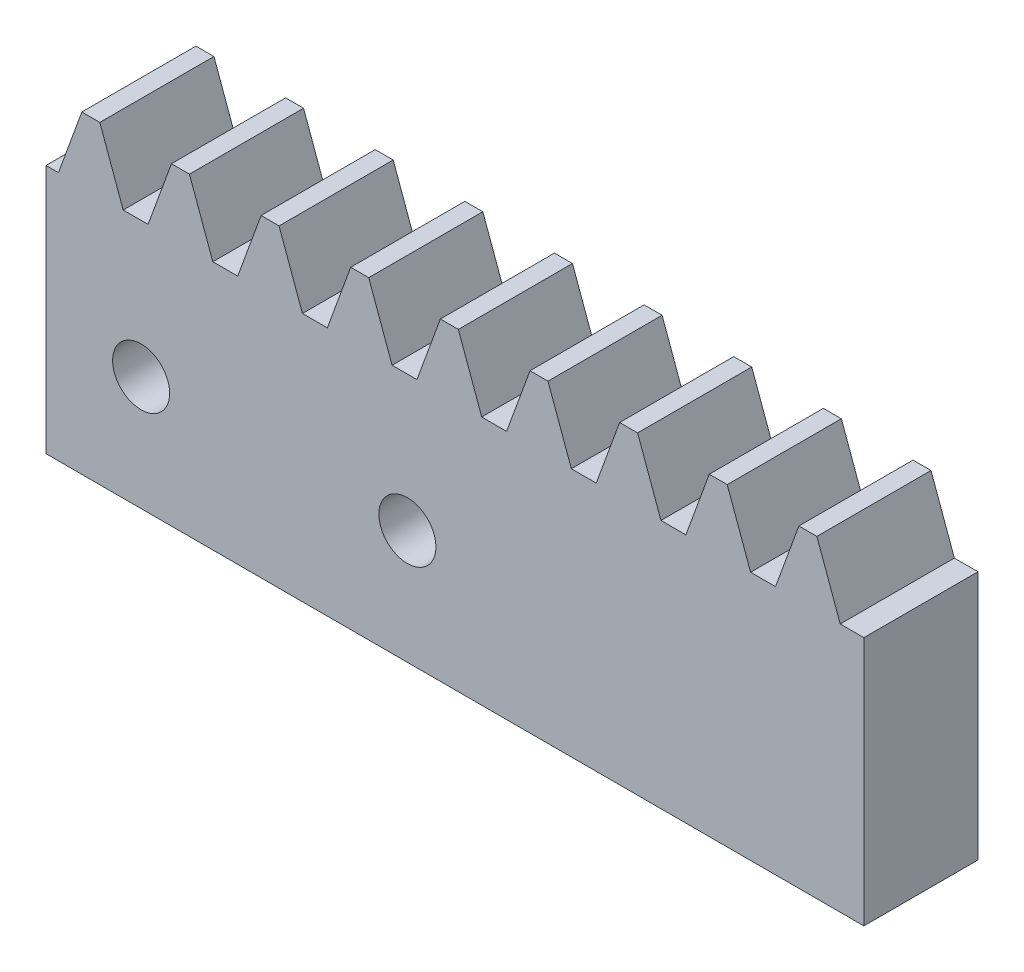
SolidWorks part; units mm, degrees
extrude "Blank" add sketch "BlankSke" against normal blind 6
sketch "BlankSke" plane through (0, 0, 0) normal (0, 0, 1) x (1, 0, 0)
  line L1 (0, 0) -> (43, 0)
  line L2 (0, 0) -> (0, 16.5)
  line L3 (0, 16.5) -> (43, 16.5)
  line L4 (43, 0) -> (43, 16.5)
  dimension "Length" = 43
  dimension "Blank_height" = 16.5
ref_plane "Plane1" through (0, 0, 0) normal (0, 0, 1) x (1, 0, 0)
ref_plane "Plane2" through (0, 0, 0) normal (0, 1, 0) x (1, 0, 0)
ref_plane "Plane3" through (0, 0, 0) normal (1, 0, 0) x (0, 0, -1)
sketch "HoldingSke" plane through (0, 0, 0) normal (0, 1, 0) x (1, 0, 0)
  line L0 (0, 0) -> (0.0928, 0.6602)
  line L1 (-15, 0) -> (100, 0) construction
  line L2 (0, 0) -> (-2.1039, 2.3779)
  line L3 (0, 0) -> (-11.863, 4.5341)
  line L4 (0, 0) -> (8.4773, 1.6478)
  line L5 (0, 0) -> (-23.7986, -8.8762)
  line L6 (0, 0) -> (-10.5278, -7.1032)
  line L9 (-71.009, 38.7566) -> (-30.6022, 53.4635)
  line L10 (-76.2, 3.8779) -> (-61.2, 3.8779)
  line L11 (0, 0) -> (-6, 0)
  line L12 (-76.2, 101.6) -> (-76.147, 101.6)
  line L13 (24.9733, 27.94) -> (52.9518, 28.4284)
  line L14 (24.9733, 27.94) -> (24.9743, 27.94)
  line L15 (24.9733, 27.94) -> (100.4006, 29.5858)
  circle A0 centre (0, 0) radius 19.05
  circle A1 centre (0, 0) radius 7.5
  circle A2 centre (0, 0) radius 12.7
  dimension "MPH" = 15
  dimension "Diameter" = 38.1
  dimension "Num_teeth" = 11
  dimension "Pitch" = 0.6667
  dimension "Show_teeth" = 998
  dimension "Thickness" = 12.7
  dimension "Ap" = 20
  dimension "Pitch_height" = 15
  dimension "Width" = 6
  dimension "Backlash" = 0.053
  dimension "Addendum_fac" = 1
  dimension "Dedendum_fac" = 1.25
  dimension "Clearance_fac" = 0.25
  dimension "Dedendum_add" = 0.001
  dimension "Length" = 43
  dimension "Module" = 1.5
sketch "TooCutSkeIll" plane through (0, 0, 0) normal (0, 0, 1) x (1, 0, 0)
  line L0 (-1.8687, 16.4605) -> (-0.7447, 13.3724)
  line L1 (-0.3914, 13.125) -> (0.3914, 13.125)
  line L2 (0.7447, 13.3724) -> (1.8687, 16.4605)
  line L3 (43, 16.5) -> (0, 16.5) construction
  line L4 (0, 0) -> (0, 64.897) construction
  line L5 (-13.208, 15) -> (12.954, 15) construction
  line L6 (0, 0) -> (43, 0) construction
  line L7 (1.3371, 15) -> (1.3371, 48.7463) construction
  line L8 (-1.3371, 15) -> (-1.3371, 48.7463) construction
  line L9 (1.9251, 16.5) -> (1.9251, 16.5254)
  line L10 (-1.9251, 16.5) -> (-1.9251, 16.5254)
  line L11 (-1.9251, 16.5254) -> (1.9251, 16.5254)
  arc A0 (0.3914, 13.125) -> (0.7447, 13.3724) centre (0.3914, 13.501) ccw
  arc A1 (-0.7447, 13.3724) -> (-0.3914, 13.125) centre (-0.3914, 13.501) ccw
  arc A2 (1.9251, 16.5) -> (1.8687, 16.4605) centre (1.9251, 16.44) ccw
  arc A3 (-1.8687, 16.4605) -> (-1.9251, 16.5) centre (-1.9251, 16.44) ccw
  dimension "Pitch_height" = 15
  dimension "Addendum_plus" = 1.5254
  dimension "Pressure_angle" = 20
  dimension "Gap_width" = 2.6742
  dimension "Dedendum" = 1.875
extrude "ToothCutIll" [suppressed] cut sketch "TooCutSkeIll" against normal through all
sketch "TooCutSkeSim" plane through (0, 0, 0) normal (0, 0, 1) x (1, 0, 0)
  line L0 (0.6547, 13.125) -> (-0.6547, 13.125)
  line L1 (1.8923, 16.5254) -> (0.6547, 13.125)
  line L2 (0, 17.4625) -> (0, 53.467) construction
  line L3 (1.8923, 16.5254) -> (-1.8923, 16.5254)
  line L6 (-1.8923, 16.5254) -> (-0.6547, 13.125)
  line L9 (-1.3371, 15) -> (1.3371, 15) construction
  line L10 (0, 0) -> (43, 0) construction
  line L11 (1.3371, 15) -> (1.3371, 53.467) construction
  line L12 (-1.3371, 15) -> (-1.3371, 53.467) construction
  dimension "Pitch_height" = 15
  dimension "Addendum_plus" = 1.5254
  dimension "Pressure_angle" = 20
  dimension "Gap_width" = 2.6742
  dimension "Dedendum" = 1.875
extrude "ToothCutSim" cut sketch "TooCutSkeSim" against normal through all
pattern_linear "TeethCuts" count 10 spacing 4.7124 along (1, 0, 0) of "ToothCutIll", "ToothCutSim"
sketch "Esquisse1" plane through (0, 0, 0) normal (0, 0, 1) x (1, 0, 0)
  line L0 (0, 13.125) -> (0, 0) construction
  line L1 (0, 0) -> (43, 0) construction
  circle A0 centre (5, 6) radius 1.5
  circle A1 centre (19, 6) radius 1.5
  dimension "D1" = 14
  dimension "D4" = 3
  dimension "D5" = 3
  dimension "D2" = 5
  dimension "D3" = 6
extrude "Enlèv. mat.-Extru.1" cut sketch "Esquisse1" against normal blind 6
equation "' \"Module@HoldingSke\" = 6.35"
equation "' \"Num_teeth@HoldingSke\" = 12"
equation "' \"Ap@HoldingSke\" =  20"
equation "' \"Ap@HoldingSke\" = 20"
equation "' \"Width@HoldingSke\" = 0.25 * 25.4"
equation "' \"Show_teeth@HoldingSke\" = 500"
equation "' \"Backlash@HoldingSke\" = 0.009 * 25.4"
equation "' \"Addendum_fac@HoldingSke\" = 1.0"
equation "' \"Dedendum_fac@HoldingSke\" = 1.25"
equation "' \"Dedendum_add@HoldingSke\" = 0.00005 * 25.4"
equation "' \"Clearance_fac@HoldingSke\" = 0.25"
equation "' \"Pitch_height@HoldingSke\" = 1 * 25.4"
equation "' \"Length@HoldingSke\" = 4.71 * 25.4"
equation "\"Pitch@HoldingSke\" = 1 / \"Module@HoldingSke\""
equation "\"MPH@HoldingSke\" = \"Dedendum_fac@HoldingSke\" / \"Pitch@HoldingSke\" + 2 * \"Dedendum_add@HoldingSke\" + 0.002 * 25.4"
equation "\"MPH@HoldingSke\" = ((sgn( \"MPH@HoldingSke\" - \"Pitch_height@HoldingSke\")+1)*( \"MPH@HoldingSke\" - \"Pitch_height@HoldingSke\"))/2 + \"Pitch_height@HoldingSke\""
equation "\"Blank_height@BlankSke\" = \"Pitch_height@HoldingSke\" + \"Addendum_fac@HoldingSke\"  / \"Pitch@HoldingSke\" "
equation "\"Length@BlankSke\" =  \"Length@HoldingSke\""
equation "\"Face_width@Blank\" = \"Width@HoldingSke\""
equation "\"Pressure_angle@TooCutSkeIll\" = \"Ap@HoldingSke\""
equation "\"Addendum_plus@TooCutSkeIll\" =  \"Addendum_fac@HoldingSke\"  / \"Pitch@HoldingSke\" + 0.001 *25.4"
equation "\"Dedendum@TooCutSkeIll\" = \"Dedendum_fac@HoldingSke\"  / \"Pitch@HoldingSke\""
equation "\"Pitch_height@TooCutSkeIll\" =  \"MPH@HoldingSke\""
equation "\"Gap_width@TooCutSkeIll\" = 3.14159265 / 2 / \"Pitch@HoldingSke\" + 6 * \"Backlash@HoldingSke\""
equation "\"Pressure_angle@TooCutSkeSim\" = \"Ap@HoldingSke\""
equation "\"Addendum_plus@TooCutSkeSim\" =  \"Addendum_fac@HoldingSke\"  / \"Pitch@HoldingSke\" + 0.001 * 25.4"
equation "\"Dedendum@TooCutSkeSim\" = \"Dedendum_fac@HoldingSke\"  / \"Pitch@HoldingSke\""
equation "\"Pitch_height@TooCutSkeSim\" =  \"MPH@HoldingSke\""
equation "\"Gap_width@TooCutSkeSim\" = 3.14159265 / 2 / \"Pitch@HoldingSke\" + 6 * \"Backlash@HoldingSke\""
equation "\"Root_fillet@TooCutSkeIll\" = \"Clearance_fac@HoldingSke\" / \"Pitch@HoldingSke\" + \"Dedendum_add@HoldingSke\""
equation "\"Break_rad@TooCutSkeIll\" = 0.02 / \"Pitch@HoldingSke\" * 2"
equation "\"Linear_pitch@TeethCuts\" = 3.14159265 / \"Pitch@HoldingSke\""
equation "\"Num_teeth@HoldingSke\" = int( ( \"Length@HoldingSke\" + 0 ) / (3.14159265 / \"Pitch@HoldingSke\")) + 0.9999  + 1"
equation " \"Num_teeth@TeethCuts\" = int( \"Show_teeth@HoldingSke\" ) + 1"
equation " \"Num_teeth@TeethCuts\" = ((sgn( \"Num_teeth@TeethCuts\" - \"Num_teeth@HoldingSke\" )-1)*( \"Num_teeth@TeethCuts\" - \"Num_teeth@HoldingSke\" ))/-2+ \"Num_teeth@HoldingSke\""
equation " \"Num_teeth@TeethCuts\" = ((sgn( \"Num_teeth@TeethCuts\" - 2.0)+1)*( \"Num_teeth@TeethCuts\" - 2.0))/2 +2.0"
